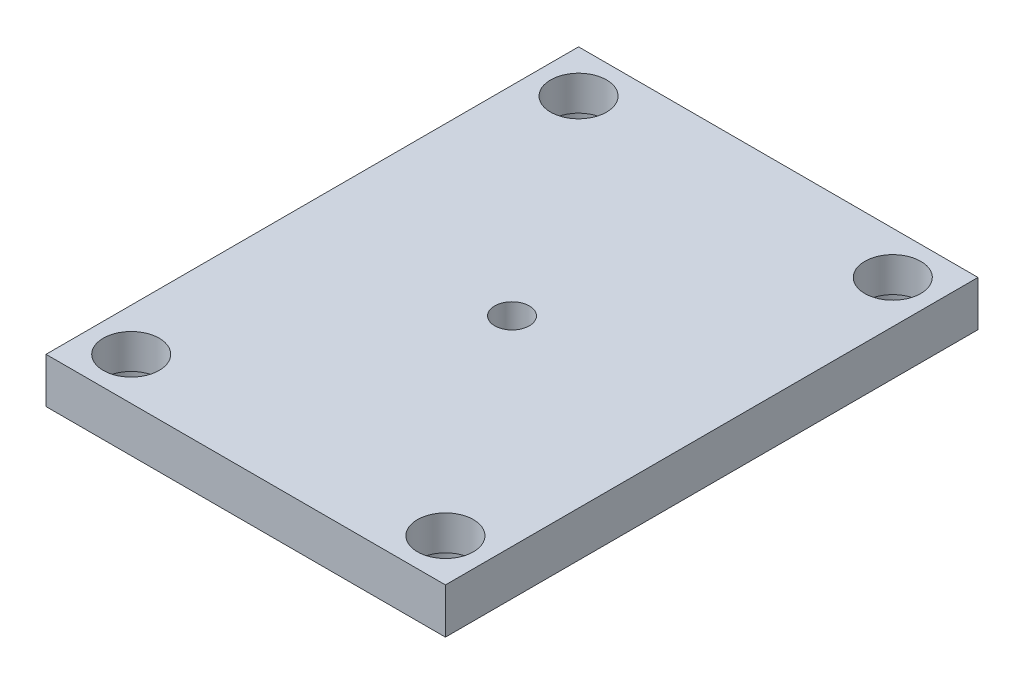
SolidWorks part; units mm, degrees
material "AISI 1020"
ref_plane "Plano frontal" through (0, 0, 0) normal (0, 0, 1) x (1, 0, 0)
ref_plane "Plano superior" through (0, 0, 0) normal (0, 1, 0) x (1, 0, 0)
ref_plane "Plano direito" through (0, 0, 0) normal (1, 0, 0) x (0, 0, -1)
sketch "Esboço1" plane through (0, 0, 0) normal (0, 1, 0) x (1, 0, 0)
  line L0 (150, 200) -> (-150, -200) construction
  line L1 (-150, 200) -> (150, 200)
  line L2 (-150, 200) -> (-150, -200)
  line L3 (-150, -200) -> (150, -200)
  line L4 (150, 200) -> (150, -200)
  circle A0 centre (0, 0) radius 13
  dimension "D1" = 300
  dimension "D2" = 400
extrude "Extrusão1" add sketch "Esboço1" along normal blind 34
hole_wizard "Furo roscado de M161" positions "Esboço3" profile "Esboço2" tap size "M16" standard "ISO"
sketch "Esboço3" plane through (0, 0, 0) normal (0, -1, 0) x (1, 0, 0)
  point P0 (-118, 119)
  point P1 (118, 119)
  point P3 (-118, -119)
  point P5 (118, -119)
  dimension "D1" = 118
  dimension "D2" = 119
  dimension "D3" = 236
  dimension "D4" = 238
sketch "Esboço2" plane through (-118, 0, 119) normal (1, 0, 0) x (0, 0, -1)
  line L0 (0, 0) -> (0, 32.206)
  line L1 (0, 32.206) -> (7, 28)
  line L2 (7, 28) -> (7, 0)
  line L5 (7, 0) -> (0, 0)
  line L10 (0, 32.206) -> (-7, 28) construction
  line L11 (0, -6.35) -> (0, 107.95) construction
  dimension "Tap Drill Dia." = 14
  dimension "Tap Drill Depth" = 28
  dimension "Drill Angle" = 118
cosmetic thread "Rosca de furo1" parameters "D1"=18, "D2"=16
cosmetic thread "Rosca de furo2" parameters "D1"=18, "D2"=16
cosmetic thread "Rosca de furo3" parameters "D1"=18, "D2"=16
cosmetic thread "Rosca de furo4" parameters "D1"=18, "D2"=16
hole_wizard "Furo1" positions "Esboço5" profile "Esboço4" legacy end condition through all
sketch "Esboço5" plane through (0, 0, 0) normal (0, -1, 0) x (1, 0, 0)
  point P0 (118, 168)
  point P1 (118, -168)
  point P3 (-118, -168)
  point P5 (-118, 168)
  dimension "D1" = 236
  dimension "D2" = 118
  dimension "D3" = 336
  dimension "D4" = 168
sketch "Esboço4" plane through (118, 0, 168) normal (1, 0, 0) x (0, 0, -1)
  line L0 (0, 0) -> (0, 34)
  line L1 (0, 34) -> (21, 34)
  line L2 (21, 34) -> (21, 8)
  line L3 (21, 8) -> (24, 8)
  line L4 (24, 8) -> (24, 0)
  line L5 (24, 0) -> (0, 0)
  line L6 (0, 110) -> (0, -10) construction
  dimension "Diameter" = 42
  dimension "Depth" = 34
  dimension "C-Bore Diameter" = 48
  dimension "C-Bore Depth" = 8
